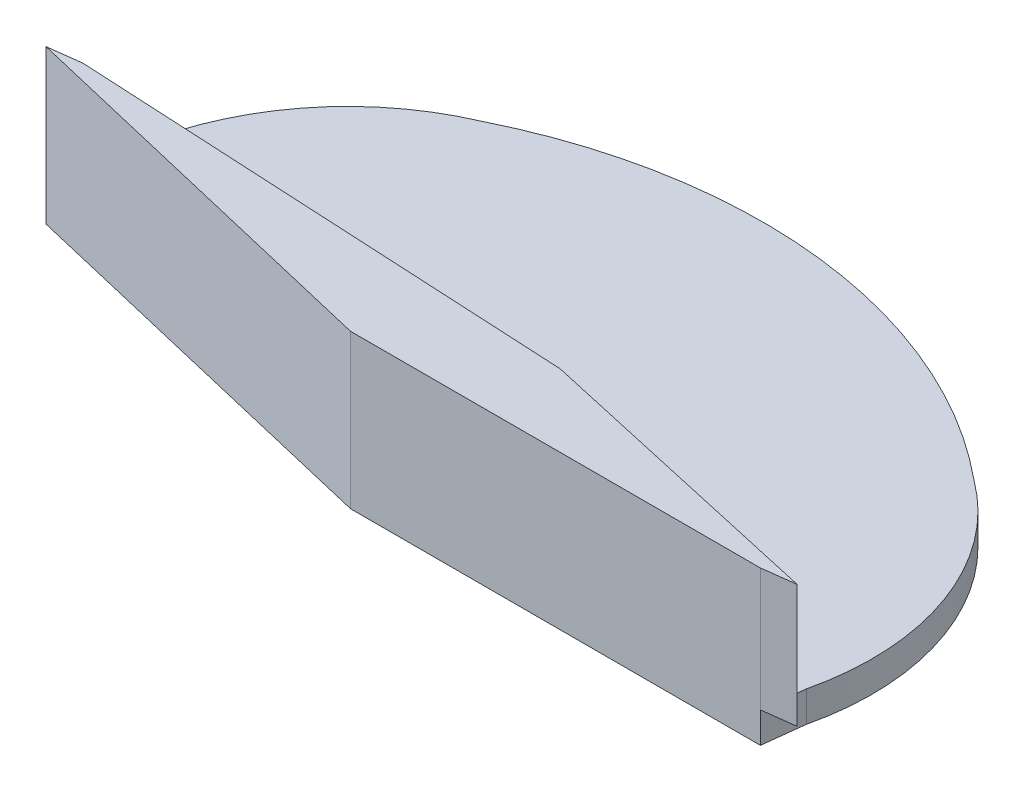
SolidWorks part; units mm, degrees
ref_plane "Alzado" through (0, 0, 0) normal (0, 0, 1) x (1, 0, 0)
ref_plane "Planta" through (0, 0, 0) normal (0, 1, 0) x (1, 0, 0)
ref_plane "Vista lateral" through (0, 0, 0) normal (1, 0, 0) x (0, 0, -1)
sketch "Croquis2" plane through (0, 0, 0) normal (0, 1, 0) x (1, 0, 0)
  line L0 (0, 0) -> (20, 0)
  line L1 (20, 0) -> (39.4636, -4.601)
  arc A0 (7.548, 11.4575) -> (0, 0) centre (12.47, 0) ccw
  arc A1 (39.4636, -4.601) -> (34.7538, 8.2856) centre (27.328, -1.7323) ccw
  arc A2 (7.548, 11.4575) -> (34.7538, 8.2856) centre (18.7047, -11.1097) cw
  dimension "D6" = 24.94
  dimension "D7" = 24.94
  dimension "D1" = 20
  dimension "D2" = 20
  dimension "D3" = 166.7
  dimension "D4" = 7.53
  dimension "D5" = 7.53
  dimension "D8" = 193.3
extrude "Saliente-Extruir2" add sketch "Croquis2" along normal blind 0.5
sketch "Croquis3" plane through (0, 0.5, 0) normal (0, 1, 0) x (1, 0, 0)
  line L0 (20, 0) -> (16.5, 0)
  line L1 (0, 0) -> (20, 0) construction
  line L2 (20, 0) -> (23.4061, -0.8052)
  line L3 (20, 0) -> (39.4636, -4.601) construction
  arc A1 (16.5, 0) -> (23.4061, -0.8052) centre (19.6222, -3.2407) cw
  dimension "D1" = 3.5
  dimension "D3" = 4.5
  dimension "D2" = 3.5
extrude "Cortar-Extruir1" cut sketch "Croquis3" against normal blind 0.5
sketch "Croquis10" plane through (0, 0, 0) normal (0, -1, 0) x (1, 0, 0)
  line L0 (20.1433, -1.229) -> (19.6222, 3.2407) construction
  line L1 (19.6222, 3.2407) -> (19.2284, 6.6178) construction
  line L2 (19.2284, 6.6178) -> (-0.2351, 2.0168)
  line L3 (19.2284, 6.6178) -> (39.2284, 6.6178)
  line L4 (-0.2351, 2.0168) -> (0, 0)
  line L5 (0, 0) -> (19.6222, -4.1248)
  line L6 (19.6222, -4.1248) -> (39.4636, 4.601)
  line L7 (39.4636, 4.601) -> (39.2284, 6.6178)
  arc A0 (16.5, 0) -> (23.4061, 0.8052) centre (19.6222, 3.2407) ccw construction
  circle A1 centre (19.6222, 3.2407) radius 3.4 construction
  circle A2 centre (19.6222, 3.2407) radius 1.5
  line M10 (39.4636, 4.601) -> (23.4061, 0.8052)
  arc M11 (23.4061, 0.8052) -> (16.5, 0) centre (19.6222, 3.2407) cw
  line M12 (16.5, 0) -> (0, 0)
  dimension "D2" = 6.8
  dimension "D7" = 3
  dimension "D1" = 4.5
  dimension "D3" = 166.7
  dimension "D4" = 83.35
  dimension "D5" = 20
  dimension "D6" = 20
extrude "Saliente-Extruir5" add sketch "Croquis10" against normal blind 0.5 contours A1 L2 L4 L7 L3 M12 M11 M10 | L2 A1 L3
sketch "Croquis11" plane through (0, 0.5, 0) normal (0, 1, 0) x (1, 0, 0)
  line L0 (19.2284, -6.6178) -> (22.5775, -4.8531) construction
  line L1 (22.5775, -4.8531) -> (25.9266, -3.0884) construction
  line L2 (25.9266, -3.0884) -> (1.3601, -1.8146)
  line L3 (-0.2351, -2.0168) -> (0, 0) construction
  line L4 (25.9266, -3.0884) -> (40.8237, -6.4156)
  line L5 (39.4636, -4.601) -> (39.2284, -6.6178) construction
  line L6 (40.8237, -6.4156) -> (39.2284, -6.6178)
  line L7 (39.2284, -6.6178) -> (19.2284, -6.6178)
  line L8 (19.2284, -6.6178) -> (-0.2351, -2.0168)
  line L9 (-0.2351, -2.0168) -> (1.3601, -1.8146)
  circle A0 centre (22.5775, -4.8531) radius 3.7856 construction
extrude "Saliente-Extruir6" add sketch "Croquis11" along normal blind 6
sketch "Croquis14" plane through (0, 0, 0) normal (0, -1, 0) x (1, 0, 0)
  line L8 (39.4636, 4.601) -> (39.2284, 6.6178)
  line L9 (39.2284, 6.6178) -> (19.2284, 6.6178)
  line L10 (19.2284, 6.6178) -> (-0.2351, 2.0168)
  line L11 (-0.2351, 2.0168) -> (0, 0)
  line L12 (39.4636, 4.601) -> (39.2284, 6.6178)
  line L13 (39.2284, 6.6178) -> (19.2284, 6.6178)
  line L14 (19.2284, 6.6178) -> (-0.2351, 2.0168)
  line L15 (-0.2351, 2.0168) -> (0, 0)
  arc A6 (34.7538, -8.2856) -> (39.4636, 4.601) centre (27.328, 1.7323) ccw
  arc A7 (0, 0) -> (7.548, -11.4575) centre (12.47, 0) ccw
  arc A8 (7.548, -11.4575) -> (34.7538, -8.2856) centre (18.7047, 11.1097) ccw
  arc A9 (34.7538, -8.2856) -> (39.4636, 4.601) centre (27.328, 1.7323) ccw
  arc A10 (0, 0) -> (7.548, -11.4575) centre (12.47, 0) ccw
  arc A11 (7.548, -11.4575) -> (34.7538, -8.2856) centre (18.7047, 11.1097) ccw
  dimension "D1" = 0
extrude "Saliente-Extruir8" add sketch "Croquis14" along normal blind 1
